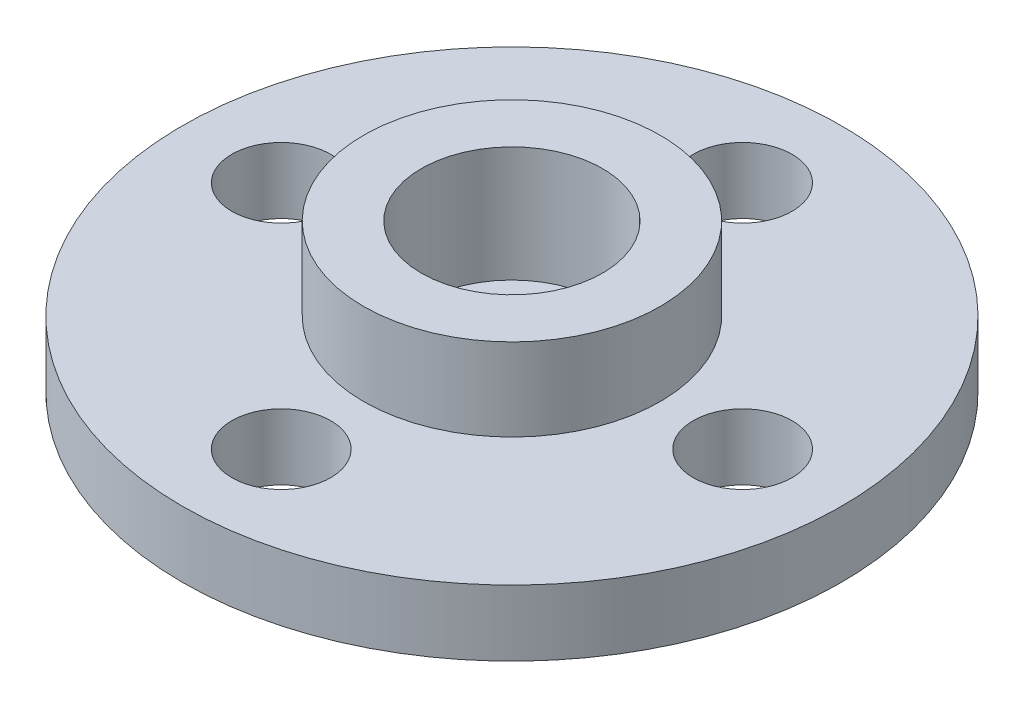
SolidWorks part; units mm, degrees
material "1060 Alloy"
ref_plane "Front Plane" through (0, 0, 0) normal (0, 0, 1) x (1, 0, 0)
ref_plane "Top Plane" through (0, 0, 0) normal (0, 1, 0) x (1, 0, 0)
ref_plane "Right Plane" through (0, 0, 0) normal (1, 0, 0) x (0, 0, -1)
sketch "Sketch1" plane through (0, 0, 0) normal (0, 1, 0) x (1, 0, 0)
  circle A0 centre (0, 0) radius 10
  dimension "D1" = 20
extrude "Boss-Extrude1" add sketch "Sketch1" along normal blind 2
sketch "Sketch2" plane through (0, 2, 0) normal (0, 1, 0) x (1, 0, 0)
  circle A0 centre (0, 0) radius 4.5
  dimension "D1" = 9
extrude "Boss-Extrude2" add sketch "Sketch2" along normal blind 2.5
sketch "Sketch3" plane through (0, 4.5, 0) normal (0, 1, 0) x (1, 0, 0)
  circle A0 centre (0, 0) radius 2.75
  dimension "D1" = 5.5
extrude "Cut-Extrude1" cut sketch "Sketch3" against normal blind 3.5
sketch "Sketch4" plane through (0, 1, 0) normal (0, 1, 0) x (1, 0, 0)
  circle A0 centre (0, 0) radius 1.5
  dimension "D1" = 3
extrude "Cut-Extrude2" cut sketch "Sketch4" against normal through all
sketch "Sketch5" plane through (0, 2, 0) normal (0, 1, 0) x (1, 0, 0)
  circle A0 centre (0, 0) radius 7 construction
  circle A1 centre (0, 7) radius 1.5
  circle A2 centre (7, 0) radius 1.5
  circle A3 centre (0, -7) radius 1.5
  circle A4 centre (-7, 0) radius 1.5
  point P14 (0, 0)
  dimension "D1" = 14
  dimension "D2" = 3
  dimension "D3" = 4
extrude "Cut-Extrude3" cut sketch "Sketch5" against normal through all
